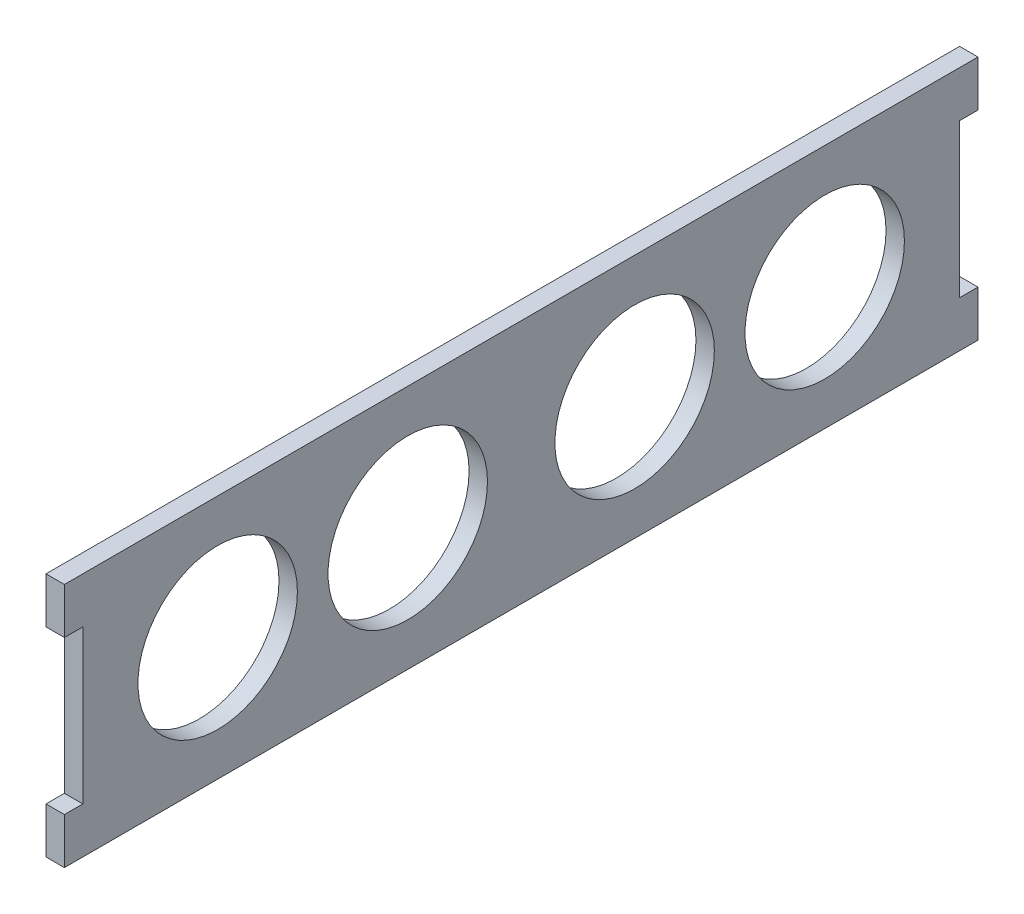
SolidWorks part; units mm, degrees
ref_plane "Front Plane" through (0, 0, 0) normal (0, 0, 1) x (1, 0, 0)
ref_plane "Top Plane" through (0, 0, 0) normal (0, 1, 0) x (1, 0, 0)
ref_plane "Right Plane" through (0, 0, 0) normal (1, 0, 0) x (0, 0, -1)
sketch "Sketch1" plane through (0, 0, 0) normal (1, 0, 0) x (0, 0, -1)
  line L0 (-74.5, 0) -> (74.5, 0) construction
  line L1 (-74.5, 20) -> (74.5, 20)
  line L2 (-74.5, 20) -> (-74.5, -20)
  line L3 (-74.5, -20) -> (74.5, -20)
  line L4 (74.5, 20) -> (74.5, -20)
  line L5 (-74.5, 12.5) -> (-71.5, 12.5)
  line L6 (-74.5, 12.5) -> (-74.5, -12.5)
  line L7 (-74.5, -12.5) -> (-71.5, -12.5)
  line L8 (-71.5, 12.5) -> (-71.5, -12.5)
  line L9 (74.5, 12.5) -> (71.5, 12.5)
  line L10 (74.5, 12.5) -> (74.5, -12.5)
  line L11 (74.5, -12.5) -> (71.5, -12.5)
  line L12 (71.5, 12.5) -> (71.5, -12.5)
  circle A0 centre (-18.5, 0) radius 13
  circle A1 centre (49.5, 0) radius 13
  circle A2 centre (-49.5, 0) radius 13
  circle A3 centre (18.5, 0) radius 13
  point P12 (-71.5, 0)
  point P13 (74.5, 0)
  point P14 (71.5, 0)
  point P23 (0, 0)
  dimension "D5" = 26
  dimension "D6" = 56
  dimension "D7" = 56
  dimension "D1" = 149
  dimension "D2" = 40
  dimension "D3" = 3
  dimension "D4" = 25
  dimension "D8" = 25
  dimension "D9" = 25
extrude "Boss-Extrude1" add sketch "Sketch1" along normal blind 3 contours L8 L0 A2 A0 A3 A1 L12 L9 L4 L1 L2 L5 | L0 L8 L7 L2 L3 L4 L11 L12 A1 A3 A0 A2
